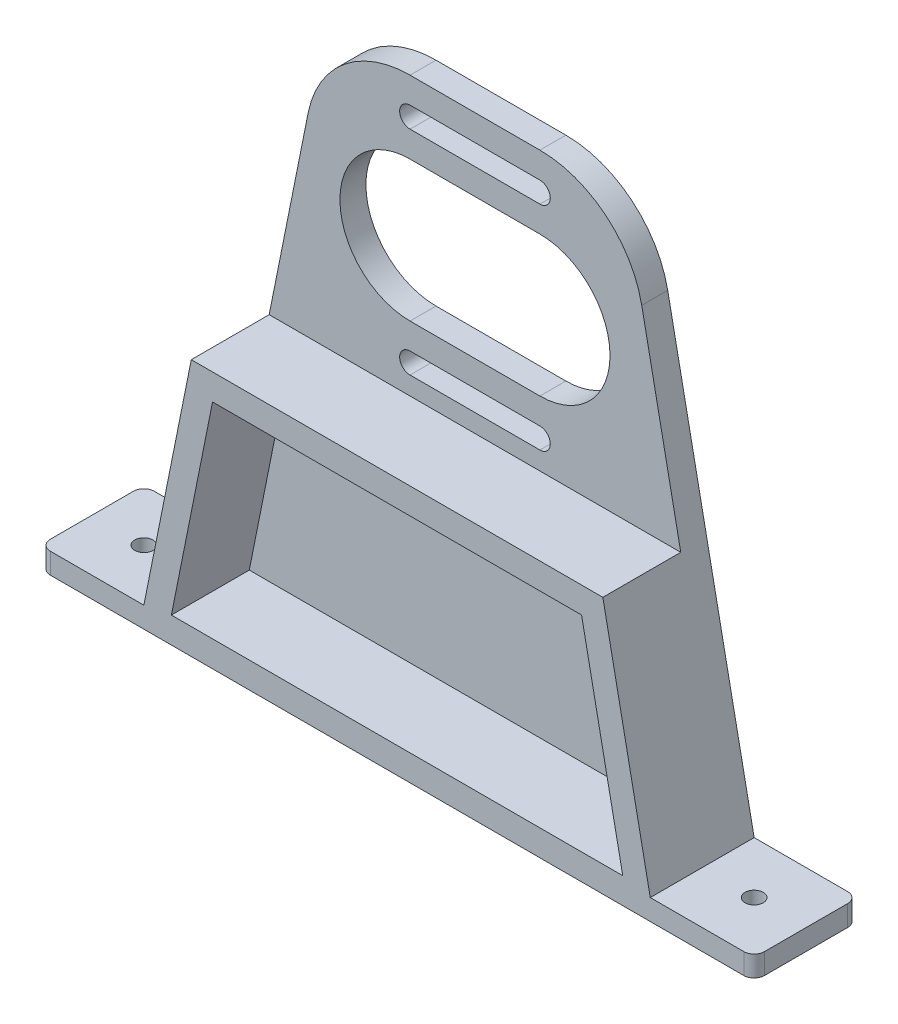
SolidWorks part; units mm, degrees
ref_plane "Front Plane" through (0, 0, 0) normal (0, 0, 1) x (1, 0, 0)
ref_plane "Top Plane" through (0, 0, 0) normal (0, 1, 0) x (1, 0, 0)
ref_plane "Right Plane" through (0, 0, 0) normal (1, 0, 0) x (0, 0, -1)
sketch "Sketch1" plane through (0, 0, 0) normal (0, 0, 1) x (1, 0, 0)
  line L0 (-68.75, 0) -> (68.75, 0)
  line L1 (-68.75, 0) -> (-68.75, 4)
  line L2 (-68.75, 4) -> (-48.75, 4)
  line L3 (-48.75, 4) -> (-32.1092, 86.9346)
  line L4 (32.1092, 86.9346) -> (48.75, 4)
  line L5 (48.75, 4) -> (68.75, 4)
  line L6 (68.75, 4) -> (68.75, 0)
  line L7 (0, 55) -> (0, 96) construction
  line L8 (-39.5201, 50) -> (39.5201, 50) construction
  line L9 (-12.5, 96) -> (12.5, 96) construction
  line L10 (-12.5, 98) -> (12.5, 98)
  line L11 (-12.5, 94) -> (12.5, 94)
  line L12 (-12.5, 75.5) -> (12.5, 75.5) construction
  line L13 (-12.5, 89) -> (12.5, 89)
  line L14 (-12.5, 62) -> (12.5, 62)
  line L15 (-12.5, 55) -> (12.5, 55) construction
  line L16 (-12.5, 57) -> (12.5, 57)
  line L17 (-12.5, 53) -> (12.5, 53)
  line L18 (-12.5, 103) -> (12.5, 103)
  line L19 (0, 96) -> (0, 103) construction
  arc A4 (-32.1092, 86.9346) -> (-12.5, 103) centre (-12.5, 83) cw
  arc A5 (-12.5, 98) -> (-12.5, 94) centre (-12.5, 96) ccw
  arc A6 (12.5, 94) -> (12.5, 98) centre (12.5, 96) ccw
  arc A7 (-12.5, 89) -> (-12.5, 62) centre (-12.5, 75.5) ccw
  arc A8 (12.5, 62) -> (12.5, 89) centre (12.5, 75.5) ccw
  arc A9 (-12.5, 57) -> (-12.5, 53) centre (-12.5, 55) ccw
  arc A10 (12.5, 53) -> (12.5, 57) centre (12.5, 55) ccw
  arc A11 (12.5, 103) -> (32.1092, 86.9346) centre (12.5, 83) cw
  circle A12 centre (0, 75.5) radius 25.5 construction
  point P13 (0, 75.5)
  point P17 (0, 96)
  point P30 (0, 55)
  point P42 (36.8479, 76.2508)
  point P43 (-12.9905, 93)
  dimension "D4" = 20
  dimension "D5" = 13.5
  dimension "D6" = 2
  dimension "D7" = 41
  dimension "D8" = 5
  dimension "D9" = 50
  dimension "D10" = 2
  dimension "D11" = 20
  dimension "D12" = 51
  dimension "D1" = 137.5
  dimension "D2" = 4
  dimension "D3" = 20
  dimension "D13" = 25
extrude "Boss-Extrude1" add sketch "Sketch1" along normal blind 5
sketch "Sketch2" plane through (0, 0, 5) normal (0, 0, 1) x (1, 0, 0)
  line L2 (-39.6204, 49.5) -> (39.6204, 49.5)
  line L3 (48.75, 4) -> (32.1092, 86.9346) construction
  line L18 (-39.6204, 49.5) -> (-48.75, 4)
  line L19 (-35.524, 44.5) -> (-43.4497, 5)
  line L23 (-35.524, 44.5) -> (35.524, 44.5)
  line L48 (-68.75, 4) -> (-68.75, 0)
  line L49 (-68.75, 0) -> (68.75, 0)
  line L50 (68.75, 0) -> (68.75, 4)
  line L51 (68.75, 4) -> (48.75, 4)
  line L52 (48.75, 4) -> (32.1092, 86.9346)
  line L53 (12.5, 103) -> (-12.5, 103)
  line L54 (-32.1092, 86.9346) -> (-48.75, 4)
  line L55 (-48.75, 4) -> (-68.75, 4)
  line L56 (-68.75, 4) -> (-68.75, 0)
  line L57 (-68.75, 0) -> (68.75, 0)
  line L58 (68.75, 0) -> (68.75, 4)
  line L59 (68.75, 4) -> (48.75, 4)
  line L60 (48.75, 4) -> (39.6204, 49.5)
  line L63 (-48.75, 4) -> (-68.75, 4)
  line L72 (-43.4497, 5) -> (43.4497, 5)
  line L73 (43.4497, 5) -> (27.2069, 85.9509)
  line L74 (12.5, 98) -> (-12.5, 98)
  line L75 (-27.2069, 85.9509) -> (-43.4497, 5)
  line L76 (-43.4497, 5) -> (43.4497, 5)
  line L77 (43.4497, 5) -> (35.524, 44.5)
  circle A4 centre (12.5, 75.5) radius 26 construction
  arc A13 (32.1092, 86.9346) -> (12.5, 103) centre (12.5, 83) ccw
  arc A14 (-12.5, 103) -> (-32.1092, 86.9346) centre (-12.5, 83) ccw
  arc A19 (27.2069, 85.9509) -> (12.5, 98) centre (12.5, 83) ccw
  arc A20 (-12.5, 98) -> (-27.2069, 85.9509) centre (-12.5, 83) ccw
  dimension "D1" = 0
  dimension "D2" = 5
  dimension "D4" = 5
  dimension "D3" = 5
  dimension "D5" = 52
extrude "Boss-Extrude2" add sketch "Sketch2" along normal offset from surface (15 mm away) 20 up to face at (0, 40.2876, 0)
sketch "Sketch4" plane through (0, 4, 0) normal (0, 1, 0) x (1, 0, 0)
  line L0 (-48.75, -10) -> (-68.75, -10) construction
  line L1 (-48.75, -20) -> (-48.75, 0) construction
  line L2 (-68.75, -20) -> (-68.75, 0) construction
  line L3 (48.75, -10) -> (68.75, -10) construction
  line L4 (48.75, -20) -> (48.75, 0) construction
  line L5 (68.75, -20) -> (68.75, 0) construction
  circle A0 centre (-58.75, -10) radius 1.75
  circle A1 centre (58.75, -10) radius 1.75
  dimension "D1" = 3.5
  dimension "D2" = 3.5
extrude "Cut-Extrude1" cut sketch "Sketch4" against normal through all
fillet "Fillet2" radius 2 4 edges at (-68.75, 2, 0) (68.75, 2, 0) (68.75, 2, 20) (-68.75, 2, 20)
